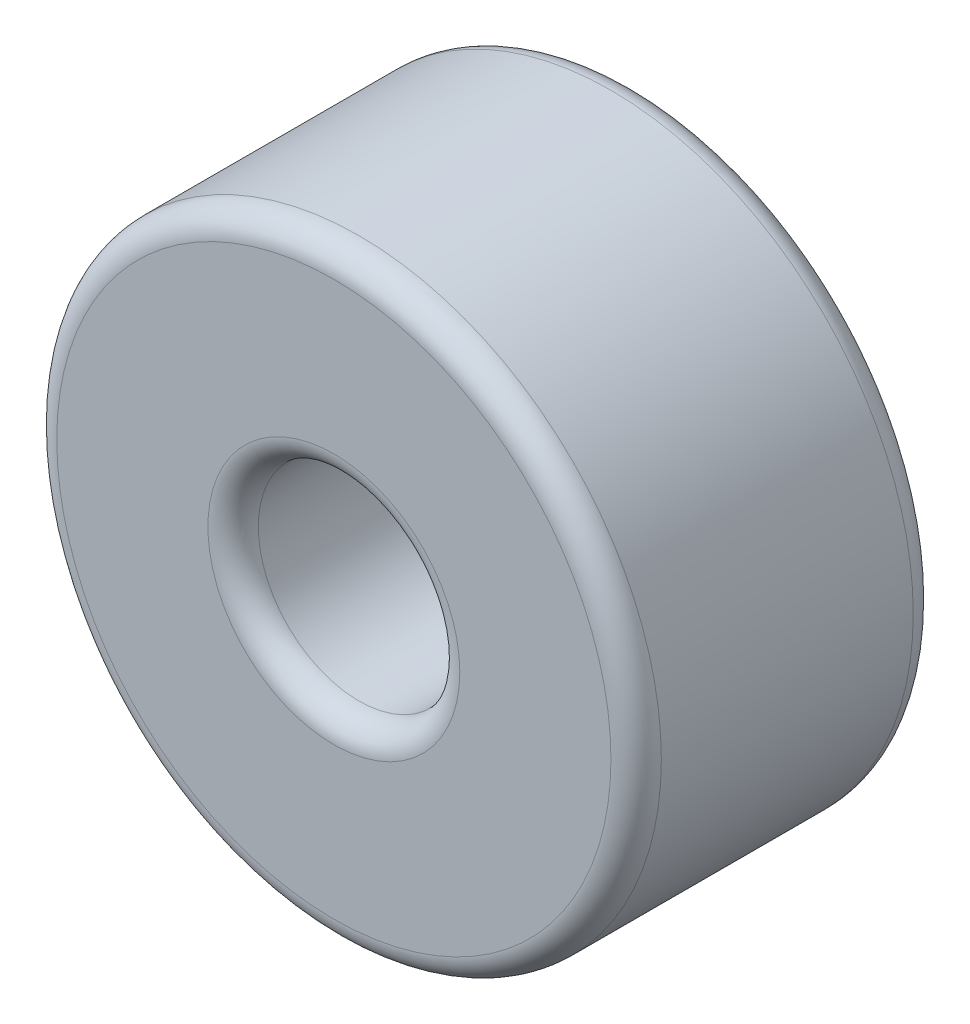
SolidWorks part; units mm, degrees
ref_plane "Front Plane" through (0, 0, 0) normal (0, 0, 1) x (1, 0, 0)
ref_plane "Top Plane" through (0, 0, 0) normal (0, 1, 0) x (1, 0, 0)
ref_plane "Right Plane" through (0, 0, 0) normal (1, 0, 0) x (0, 0, -1)
sketch "Sketch1" plane through (0, 0, 0) normal (0, 0, 1) x (1, 0, 0)
  circle A0 centre (0, 0) radius 1
  dimension "D1" = 2
extrude "Extrude-Thin1" add sketch "Sketch1" along normal blind 3 thin
fillet "Fillet2" radius 0.25 4 edges at (1, 0, 3) (3, 0, 3) (1, 0, 0) (3, 0, 0)
